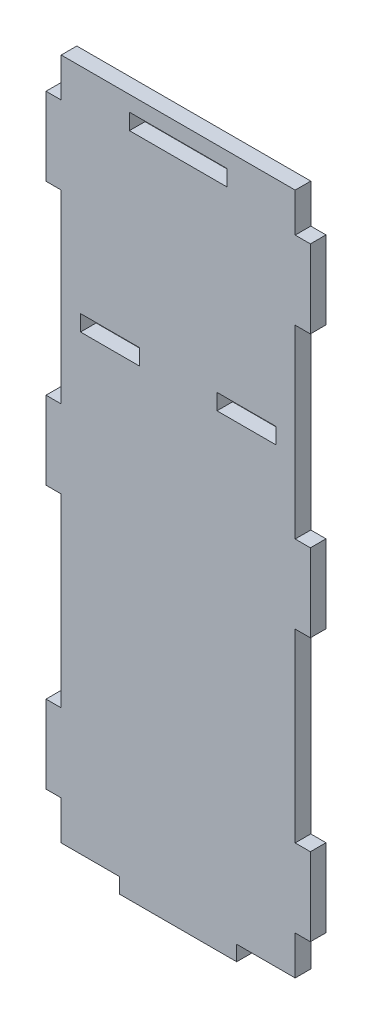
SolidWorks part; units mm, degrees
material "MDF"
ref_plane "正面" through (0, 0, 0) normal (1, 0, 0) x (0, 1, 0)
ref_plane "平面" through (0, 0, 0) normal (0, 0, 1) x (0, 1, 0)
ref_plane "右側面" through (0, 0, 0) normal (0, 1, 0) x (-1, 0, 0)
sketch "ｽｹｯﾁ1" plane through (0, 0, 0) normal (0, 0, 1) x (0, 1, 0)
  line L0 (165, 63.9) -> (145, 63.9)
  line L1 (0, 0) -> (175, 0)
  line L2 (0, 0) -> (0, 60)
  line L3 (0, 60) -> (175, 60)
  line L4 (175, 0) -> (175, 60)
  line L5 (87.5, 60) -> (87.5, 0) construction
  line L6 (0, 30) -> (175, 30) construction
  line L7 (10, 60) -> (30, 60)
  line L8 (10, 60) -> (10, 63.9)
  line L9 (10, 63.9) -> (30, 63.9)
  line L10 (30, 60) -> (30, 63.9)
  line L11 (77.5, 60) -> (97.5, 60)
  line L12 (77.5, 60) -> (77.5, 63.9)
  line L13 (77.5, 63.9) -> (97.5, 63.9)
  line L14 (97.5, 60) -> (97.5, 63.9)
  line L19 (145, 60) -> (145, 63.9)
  line L20 (165, 60) -> (145, 60)
  line L21 (165, 60) -> (165, 63.9)
  line L22 (165, 0) -> (165, -3.9)
  line L23 (165, 0) -> (145, 0)
  line L24 (145, 0) -> (145, -3.9)
  line L25 (165, -3.9) -> (145, -3.9)
  line L26 (10, -3.9) -> (30, -3.9)
  line L27 (30, 0) -> (30, -3.9)
  line L28 (10, 0) -> (30, 0)
  line L29 (10, 0) -> (10, -3.9)
  line L30 (77.5, -3.9) -> (97.5, -3.9)
  line L31 (97.5, 0) -> (97.5, -3.9)
  line L32 (77.5, 0) -> (97.5, 0)
  line L33 (77.5, 0) -> (77.5, -3.9)
  line L35 (0, 15) -> (-3.9, 15)
  line L36 (0, 15) -> (0, 45)
  line L37 (0, 45) -> (-3.9, 45)
  line L38 (-3.9, 15) -> (-3.9, 45)
  line L39 (0, 15) -> (-3.9, 45) construction
  line L40 (0, 45) -> (-3.9, 15) construction
  line L44 (115.95, 20.05) -> (120.05, 20.05)
  line L45 (115.95, 55.05) -> (120.05, 55.05)
  line L46 (115.95, 55.05) -> (115.95, 39.95)
  line L47 (115.95, 39.95) -> (120.05, 39.95)
  line L48 (120.05, 55.05) -> (120.05, 39.95)
  line L49 (115.95, 55.05) -> (120.05, 39.95) construction
  line L50 (115.95, 39.95) -> (120.05, 55.05) construction
  line L51 (120.05, 4.95) -> (120.05, 20.05)
  line L52 (115.95, 4.95) -> (120.05, 4.95)
  line L53 (115.95, 4.95) -> (115.95, 20.05)
  line L55 (166.95, 42.5) -> (171.05, 42.5)
  line L56 (166.95, 42.5) -> (166.95, 17.5)
  line L57 (166.95, 17.5) -> (171.05, 17.5)
  line L58 (171.05, 42.5) -> (171.05, 17.5)
  line L59 (166.95, 42.5) -> (171.05, 17.5) construction
  line L60 (166.95, 17.5) -> (171.05, 42.5) construction
  point P16 (87.5, 63.9)
  point P33 (-1.95, 30)
  point P38 (118, 47.5)
  point P47 (169, 30)
  point P48 (0, 0)
  point P116 (87.5, 30)
  dimension "D1" = 175
  dimension "D2" = 60
  dimension "D3" = 10
  dimension "D4" = 20
  dimension "D5" = 3.9
  dimension "D6" = 20
  dimension "D7" = 3.9
  dimension "D8" = 30
  dimension "D9" = 3.9
  dimension "D10" = 15.1
  dimension "D11" = 4.1
  dimension "D12" = 118
  dimension "D13" = 17.5
  dimension "D14" = 4.1
  dimension "D15" = 25
  dimension "D16" = 6
extrude "ﾎﾞｽ - 押し出し1" add sketch "ｽｹｯﾁ1" along normal blind 4 contours L1 L4 L3 L2 | L1 L29 L26 L27 | L25 L22 L1 L24
equation "\"D6@ｽｹｯﾁ1\"= \"D4@ｽｹｯﾁ1\""
equation "\"D7@ｽｹｯﾁ1\"= \"D5@ｽｹｯﾁ1\""
